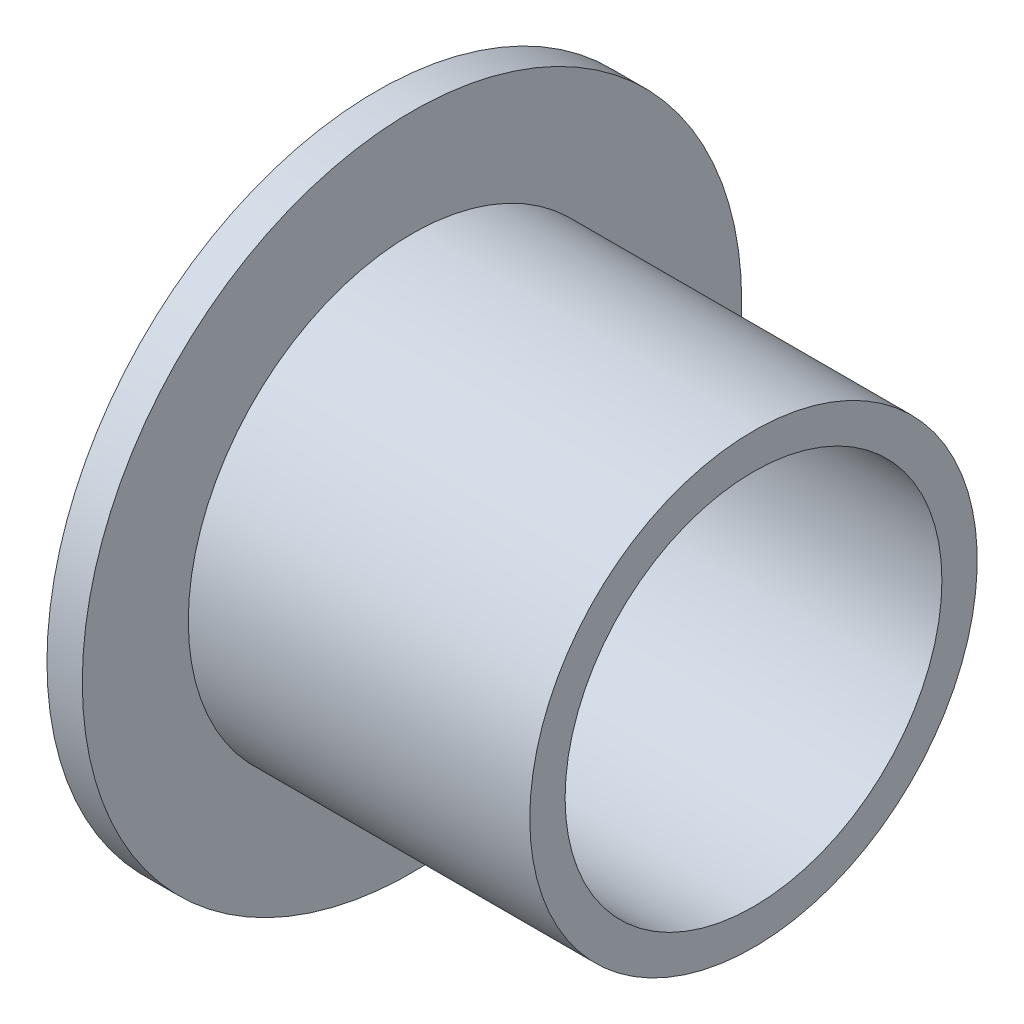
SolidWorks part; units mm, degrees
material "PTFE (general)"
ref_plane "Front Plane" through (0, 0, 0) normal (0, 0, 1) x (1, 0, 0)
ref_plane "Top Plane" through (0, 0, 0) normal (0, 1, 0) x (1, 0, 0)
ref_plane "Right Plane" through (0, 0, 0) normal (1, 0, 0) x (0, 0, -1)
sketch "Sketch2" plane through (0, 0, 0) normal (0, 0, 1) x (1, 0, 0)
  line L0 (-1.1906, 11.1125) -> (-1.1906, 6.35)
  line L1 (-1.1906, 6.35) -> (11.5094, 6.35)
  line L2 (11.5094, 6.35) -> (11.5094, 7.5406)
  line L3 (11.5094, 7.5406) -> (0, 7.5406)
  line L4 (0, 7.5406) -> (0, 11.1125)
  line L5 (0, 11.1125) -> (-1.1906, 11.1125)
  line L6 (0, 0) -> (59.9113, 0) construction
  dimension "D1" = 22.225
  dimension "D2" = 12.7
  dimension "D3" = 15.0812
  dimension "D4" = 12.7
  dimension "D5" = 1.1906
revolve "Revolve1" add sketch "Sketch2" angle 360 about L6
